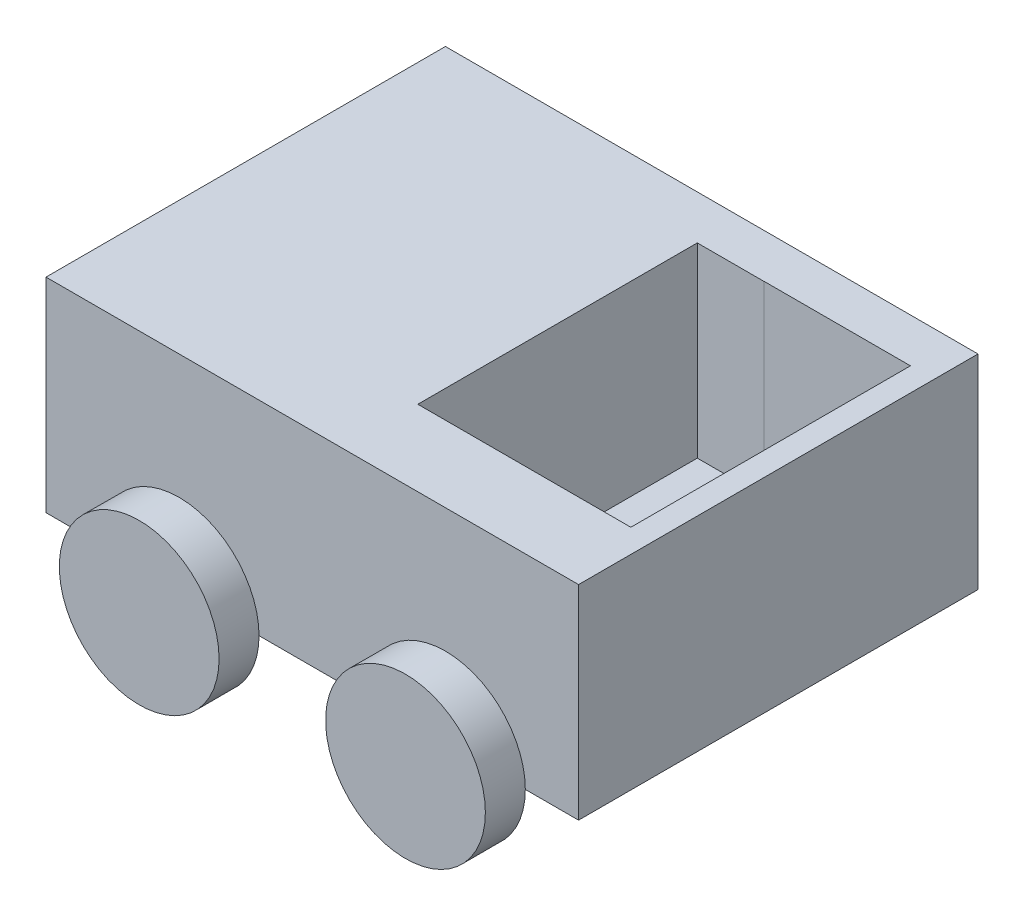
SolidWorks part; units mm, degrees
ref_plane "Front Plane" through (0, 0, 0) normal (0, 0, 1) x (1, 0, 0)
ref_plane "Top Plane" through (0, 0, 0) normal (0, 1, 0) x (1, 0, 0)
ref_plane "Right Plane" through (0, 0, 0) normal (1, 0, 0) x (0, 0, -1)
sketch "Sketch7" plane through (0, 0, 0) normal (0, 0, 1) x (1, 0, 0)
  line L1 (0, 0) -> (20, 0)
  line L2 (0, 0) -> (0, -7.663)
  line L3 (0, -7.663) -> (20, -7.663)
  line L4 (20, 0) -> (20, -7.663)
  dimension "D2" = 20
extrude "Boss-Extrude2" add sketch "Sketch7" along normal blind 15 contours L1 L4 L3 L2
sketch "Sketch8" plane through (0, 0, 0) normal (0, 1, 0) x (1, 0, 0)
  line L0 (19.1173, -1.6543) -> (13.6173, -1.6543)
  line L3 (13.6173, -12.1543) -> (19.1173, -12.1543)
  line L4 (19.1173, -1.6543) -> (19.1173, -12.1543)
  line L5 (13.6173, -1.6543) -> (13.6173, -12.1543)
extrude "Cut-Extrude3" cut sketch "Sketch8" against normal blind 7 contours L5 L3 L4 L0
sketch "Sketch9" plane through (0, 0, 15) normal (0, 0, 1) x (1, 0, 0)
  circle A1 centre (5, -7.663) radius 3
  circle A3 centre (15, -7.663) radius 3
extrude "Boss-Extrude4" add sketch "Sketch9" along normal blind 1.5 contours A3
sketch "Sketch11" plane through (0, 0, 15) normal (0, 0, 1) x (1, 0, 0)
  circle A1 centre (5, -7.663) radius 3
extrude "Boss-Extrude6" add sketch "Sketch11" along normal blind 1.5
sketch "Sketch12" plane through (0, 0, 0) normal (0, 0, -1) x (-1, 0, 0)
  circle A1 centre (-15, -7.663) radius 3
  circle A3 centre (-5, -7.663) radius 3
extrude "Boss-Extrude7" add sketch "Sketch12" along normal blind 1.5
sketch "Sketch13" plane through (0, 0, 0) normal (0, 1, 0) x (1, 0, 0)
  line L1 (13.6173, -12.1543) -> (11.1173, -12.1543)
  line L2 (13.6173, -12.1543) -> (13.6173, -1.6584)
  line L3 (13.6173, -1.6584) -> (11.1173, -1.6584)
  line L4 (11.1173, -12.1543) -> (11.1173, -1.6584)
  dimension "D1" = 90
extrude "Cut-Extrude4" cut sketch "Sketch13" against normal blind 7
